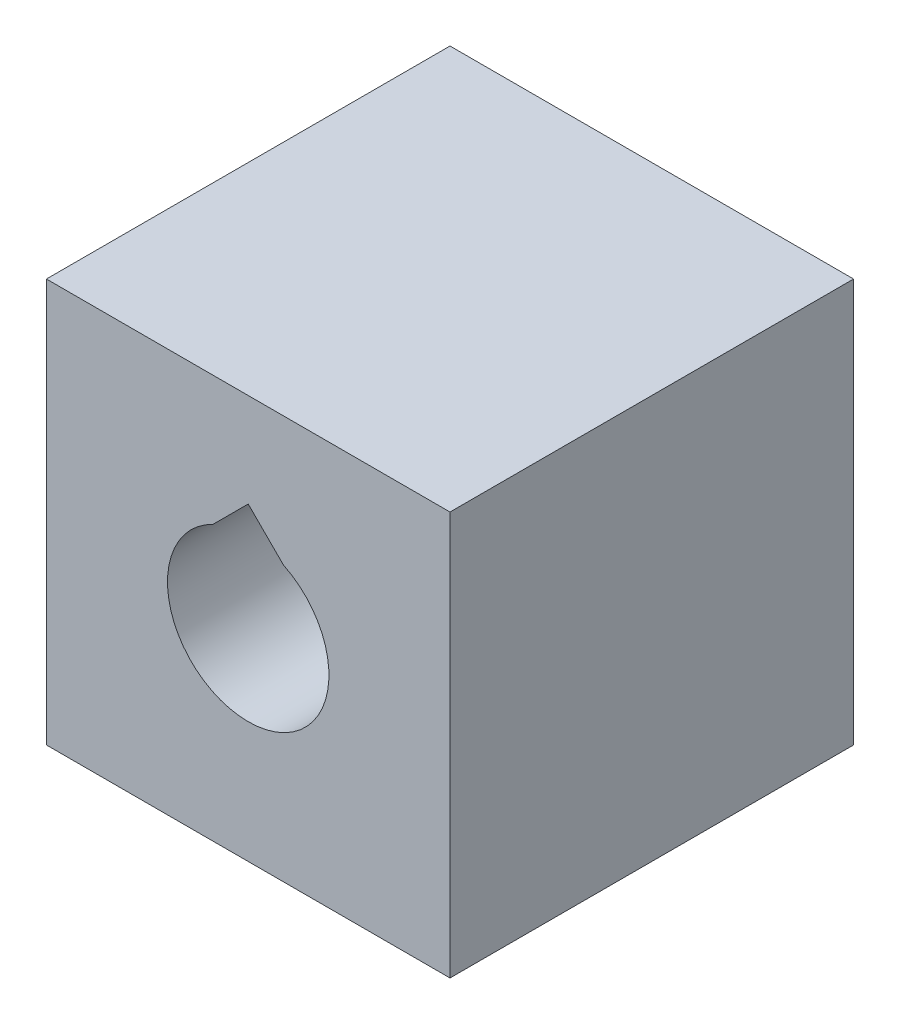
SolidWorks part; units mm, degrees
ref_plane "Front Plane" through (0, 0, 0) normal (0, 0, 1) x (1, 0, 0)
ref_plane "Top Plane" through (0, 0, 0) normal (0, 1, 0) x (1, 0, 0)
ref_plane "Right Plane" through (0, 0, 0) normal (1, 0, 0) x (0, 0, -1)
sketch "Sketch1" plane through (0, 0, 0) normal (0, 1, 0) x (1, 0, 0)
  line L5 (12.5, -12.5) -> (-12.5, -12.5)
  line L6 (12.5, -12.5) -> (12.5, 12.5)
  line L7 (12.5, 12.5) -> (-12.5, 12.5)
  line L8 (-12.5, -12.5) -> (-12.5, 12.5)
  line L9 (12.5, -12.5) -> (-12.5, 12.5) construction
  line L10 (12.5, 12.5) -> (-12.5, -12.5) construction
  point P0 (0, 0)
  dimension "D1" = 25
  dimension "D2" = 25
extrude "Boss-Extrude1" add sketch "Sketch1" along normal blind 25
sketch "Sketch2" plane through (0, 0, 12.5) normal (0, 0, 1) x (1, 0, 0)
  line L0 (0, 0) -> (0, 25) construction
  line L1 (-12.5, 25) -> (12.5, 25) construction
  line L2 (-2.1794, 17) -> (2.1794, 17) construction
  line L3 (-2.1794, 17) -> (0, 19.1794)
  line L4 (2.1794, 17) -> (0, 19.1794)
  circle A0 centre (0, 12.5) radius 5 construction
  arc A1 (-2.1794, 17) -> (2.1794, 17) centre (0, 12.5) ccw
  dimension "D1" = 10
  dimension "D2" = 4.5
  dimension "D3" = 45
extrude "Cut-Extrude1" cut sketch "Sketch2" against normal through all
